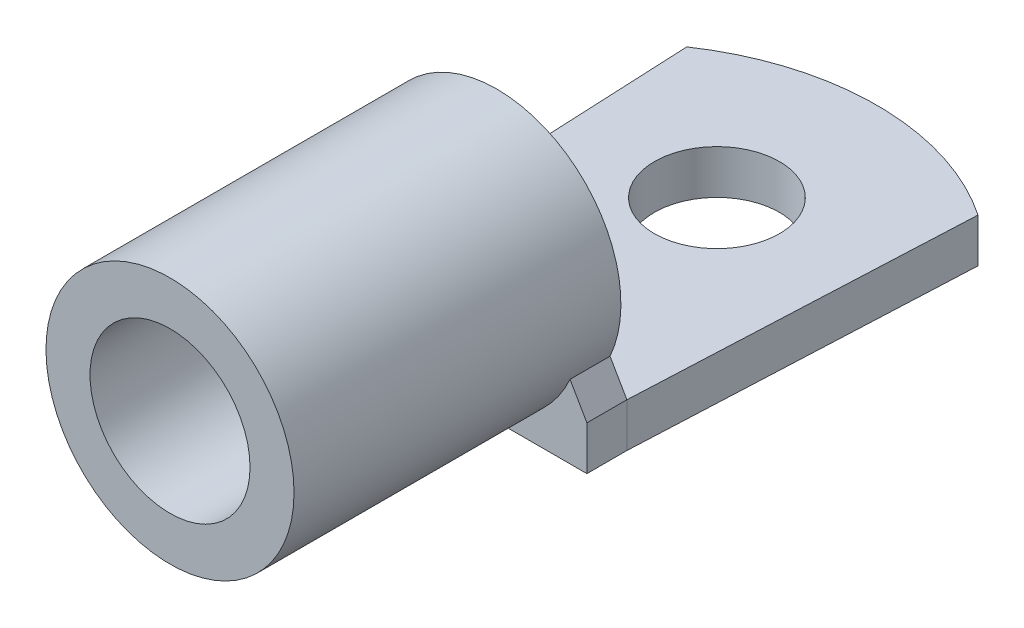
SolidWorks part; units mm, degrees
material "Copper"
ref_plane "Front Plane" through (0, 0, 0) normal (0, 0, 1) x (1, 0, 0)
ref_plane "Top Plane" through (0, 0, 0) normal (0, 1, 0) x (1, 0, 0)
ref_plane "Right Plane" through (0, 0, 0) normal (1, 0, 0) x (0, 0, -1)
sketch "Sketch1" plane through (0, 0, 0) normal (0, 1, 0) x (1, 0, 0)
  line L0 (-9.2456, 7.3284) -> (-8.255, -13.97)
  line L1 (9.2456, 7.3284) -> (8.255, -13.97)
  line L2 (0, 0) -> (0, -6.35) construction
  line L3 (-9.2456, 7.3284) -> (9.2456, 7.3284) construction
  line L4 (-8.255, -13.97) -> (8.255, -13.97)
  circle A0 centre (0, 0) radius 3.9688
  arc A1 (-9.2456, 7.3284) -> (9.2456, 7.3284) centre (0, -6.35) cw
  point P8 (0, -13.97)
  dimension "D1" = 7.9375
  dimension "D2" = 16.51
  dimension "D3" = 6.35
  dimension "D4" = 18.4912
  dimension "D5" = 16.51
  dimension "D6" = 13.97
extrude "Lug" add sketch "Sketch1" along normal blind 2.794
sketch "Sketch2" plane through (0, 0, 13.97) normal (0, 0, 1) x (1, 0, 0)
  line L0 (-8.255, 0) -> (8.255, 0) construction
  line L1 (0, 7.874) -> (0, 0) construction
  line L2 (-8.255, 2.794) -> (8.255, 2.794) construction
  circle A0 centre (0, 7.874) radius 7.874
  circle A1 centre (0, 7.874) radius 5.08
  dimension "D1" = 10.16
extrude "Crimp Socket" add sketch "Sketch2" along normal blind 20.7518
sketch "Sketch3" plane through (0, 0, 13.97) normal (0, 0, 1) x (1, 0, 0)
  line L1 (8.255, 2.794) -> (8.255, 0) construction
  line L2 (0, 0) -> (8.255, 0) construction
  line L3 (-8.255, 0) -> (0, 0) construction
  line L4 (-8.255, 2.794) -> (-8.255, 0) construction
  line L6 (6.0161, 2.794) -> (8.255, 2.794) construction
  line L7 (8.255, 2.794) -> (8.255, 0)
  line L8 (0, 0) -> (8.255, 0)
  line L9 (-8.255, 0) -> (0, 0)
  line L10 (-8.255, 2.794) -> (-8.255, 0)
  line L11 (7.1836, 4.6497) -> (-7.1836, 4.6497) construction
  line L12 (-8.255, 2.794) -> (-7.1836, 4.6497)
  line L13 (8.255, 2.794) -> (7.1836, 4.6497)
  line L14 (-8.255, 2.794) -> (-6.0161, 2.794) construction
  line L15 (6.0161, 2.794) -> (8.255, 2.794)
  line L16 (-8.255, 2.794) -> (-6.0161, 2.794)
  arc A0 (6.0161, 2.794) -> (-6.0161, 2.794) centre (0, 7.874) ccw construction
  arc A1 (6.0161, 2.794) -> (-6.0161, 2.794) centre (0, 7.874) ccw
  arc M1 (6.0161, 2.794) -> (0, 0) centre (0, 7.874) cw
  line M2 (0, 0) -> (8.255, 0)
  line M3 (8.255, 0) -> (8.255, 2.794)
  line M4 (8.255, 2.794) -> (6.0161, 2.794)
  dimension "D1" = 60
extrude "Lug Socket Connection" add sketch "Sketch3" along normal blind 2.54 contours A1 L13 M4 | A1 L12 L16 | M4 M1 M2 M3 | A1 L11 L16 L10 L9 M1 | L11 A1
